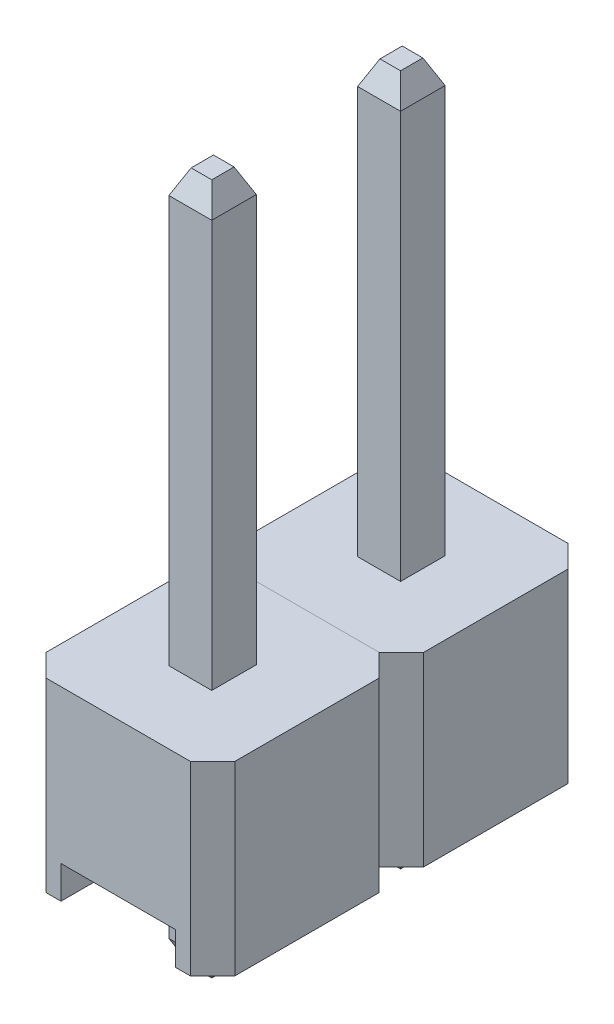
SolidWorks part; units mm, degrees
material "Latón"
ref_plane "Alzado" through (0, 0, 0) normal (0, 0, 1) x (1, 0, 0)
ref_plane "Planta" through (0, 0, 0) normal (0, 1, 0) x (1, 0, 0)
ref_plane "Vista lateral" through (0, 0, 0) normal (1, 0, 0) x (0, 0, -1)
sketch "Croquis1" plane through (0, 0, 0) normal (0, 1, 0) x (1, 0, 0)
  line L0 (0.3, 0) -> (2.24, 0)
  line L1 (2.54, 0.3) -> (2.54, 2.24)
  line L2 (2.24, 2.54) -> (0.3, 2.54)
  line L3 (0, 2.24) -> (0, 0.3)
  line L4 (0.3, 2.54) -> (0, 2.24)
  line L5 (2.54, 2.24) -> (2.24, 2.54)
  line L6 (2.24, 0) -> (2.54, 0.3)
  line L7 (0, 0.3) -> (0.3, 0)
  point P0 (0, 0)
  point P1 (2.54, 0)
  point P2 (0, 2.54)
  point P3 (2.54, 2.54)
  dimension "D1" = 0.3
  dimension "D2" = 45
  dimension "D3" = 0.3
  dimension "D4" = 45
  dimension "D5" = 0.3
  dimension "D6" = 45
  dimension "D7" = 0.3
  dimension "D8" = 45
extrude "Cuerpo Plástico" add sketch "Croquis1" along normal blind 2.5
sketch "Croquis2" plane through (0, 0, 0) normal (0, -1, 0) x (1, 0, 0)
  line L0 (0.5, 0) -> (0.5, -2.54)
  line L3 (0, -2.24) -> (0, -0.3) construction
  line L4 (2.04, 0) -> (2.04, -2.54)
  line L7 (2.54, -0.3) -> (2.54, -2.24) construction
  line L8 (0.5, 0) -> (2.04, 0)
  line L9 (0.5, -2.54) -> (2.04, -2.54)
  dimension "D1" = 0.5
  dimension "D2" = 0.5
  dimension "D3" = 1.54
extrude "Ranura" cut sketch "Croquis2" against normal blind 0.44
sketch "Croquis3" plane through (0, 2.5, 0) normal (0, 1, 0) x (1, 0, 0)
  line L0 (0.9812, 1.57) -> (1.5588, 1.57)
  line L1 (1.27, 2.54) -> (1.27, 1.57) construction
  line L2 (2.24, 2.54) -> (0.3, 2.54) construction
  line L3 (1.5588, 1.57) -> (1.5588, 0.97)
  line L4 (1.5588, 0.97) -> (0.9812, 0.97)
  line L5 (0.9812, 0.97) -> (0.9812, 1.57)
  line L6 (0, 1.27) -> (0.9812, 1.27) construction
  line L7 (0, 2.24) -> (0, 0.3) construction
  dimension "D1" = 0.6
extrude "Pin" add sketch "Croquis3" along normal blind 5.8 and the other way blind 3.5
chamfer "Chaflán1" distance 0.15 angle 65 4 edges at (1.27, 8.3, -1.57) (1.5588, 8.3, -1.27) (1.27, 8.3, -0.97) (0.9812, 8.3, -1.27)
chamfer "Chaflán2" distance 0.15 angle 65 4 edges at (1.27, -1, -0.97) (1.5588, -1, -1.27) (1.27, -1, -1.57) (0.9812, -1, -1.27)
sketch "Dirección" plane through (0, 0, 0) normal (-1, 0, 0) x (0, 0, 1)
  line L0 (-2.24, 1.25) -> (-0.3, 1.25) construction
  line L1 (-2.24, 2.5) -> (-2.24, 0) construction
  line L2 (-0.3, 2.5) -> (-0.3, 0) construction
sketch "Dirección 2" plane through (0, 0, -2.54) normal (0, 0, -1) x (-1, 0, 0)
  line L0 (-2.24, 1.25) -> (-0.3, 1.25) construction
  line L1 (-2.24, 2.5) -> (-2.24, 0) construction
  line L2 (-0.3, 2.5) -> (-0.3, 0) construction
pattern_linear "Matriz" count 2 spacing 2.54 along (0, 0, 1) of bodies 103
other "PropertyManager"
